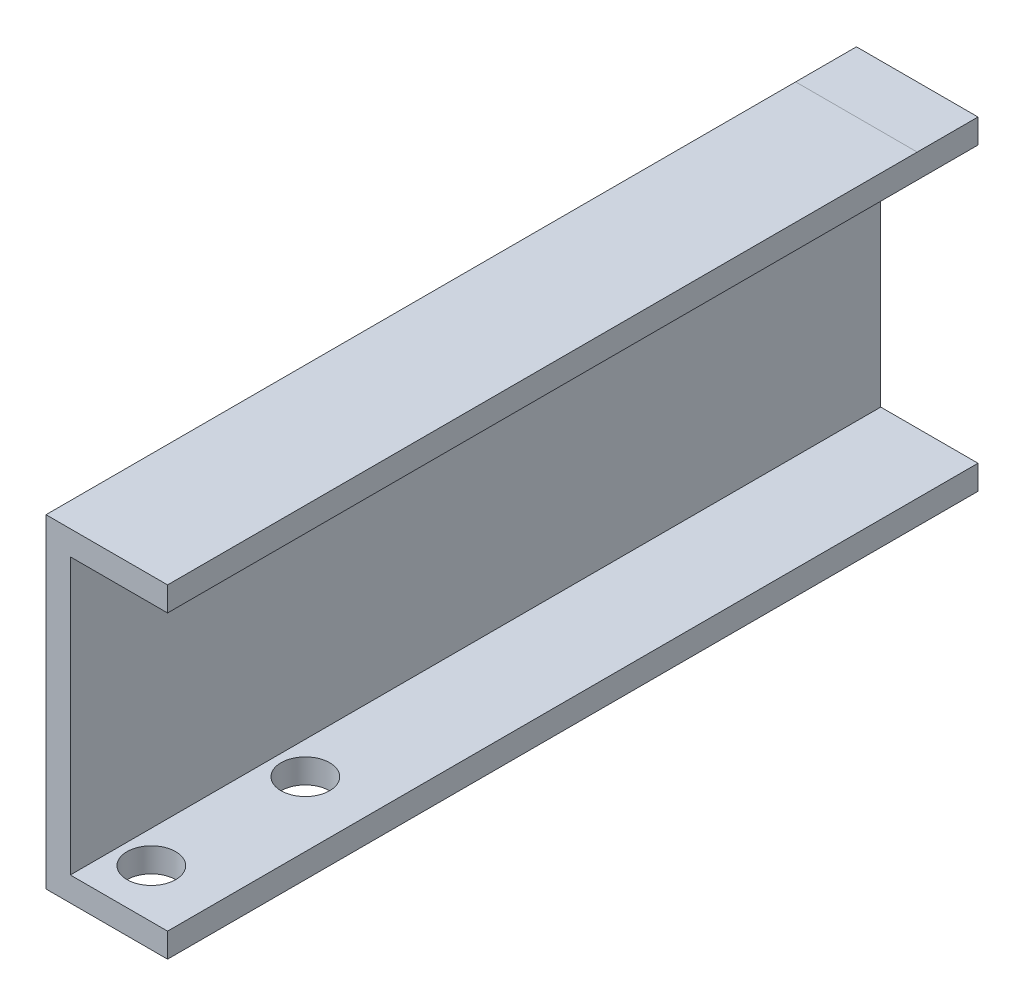
SolidWorks part; units mm, degrees
ref_plane "Ebene vorne" through (0, 0, 0) normal (0, 0, 1) x (1, 0, 0)
ref_plane "Ebene oben" through (0, 0, 0) normal (0, 1, 0) x (1, 0, 0)
ref_plane "Ebene rechts" through (0, 0, 0) normal (1, 0, 0) x (0, 0, -1)
sketch "Skizze1" plane through (0, 0, 0) normal (0, 0, 1) x (1, 0, 0)
  line L0 (0, 0) -> (39.6498, 0) construction
  line L1 (30, 40) -> (0, 40)
  line L2 (0, 40) -> (0, -40)
  line L3 (0, -40) -> (30, -40)
  point P5 (0, 0)
  dimension "D1" = 30
  dimension "D2" = 80
extrude "Linear-Austragen-Dünn1" add sketch "Skizze1" against normal blind 200 thin thin type one direction reverse wall 6
ref_plane "Ebene1" through (0, 0, -185) normal (0, 0, 1) x (1, 0, 0)
ref_plane "Ebene2" through (0, 0, -60) normal (0, 0, 1) x (1, 0, 0)
split line "Trennlinie2"
split line "Trennlinie3"
sketch "Skizze2" plane through (0, 0, 0) normal (0, 1, 0) x (1, 0, 0)
  circle A0 centre (14, 50) radius 6
  circle A1 centre (14, 12) radius 6
  dimension "D1" = 12
  dimension "D2" = 14
  dimension "D3" = 12
  dimension "D4" = 50
extrude "Schnitt-Linear austragen1" cut sketch "Skizze2" against normal blind 60
